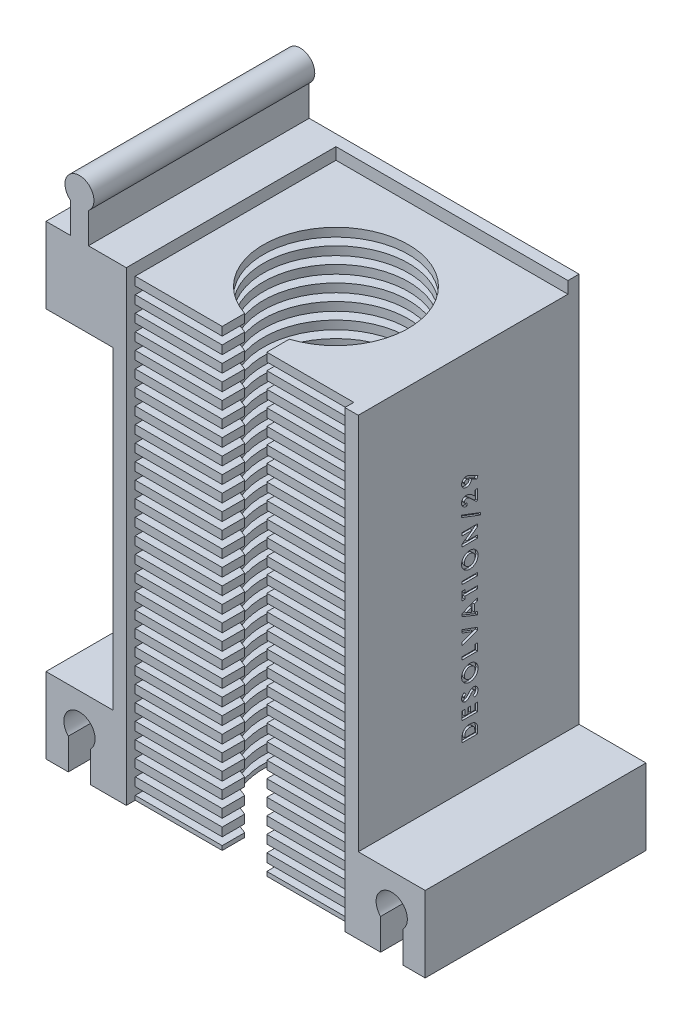
SolidWorks part; units mm, degrees
ref_plane "Plan de face" through (0, 0, 0) normal (0, 0, 1) x (1, 0, 0)
ref_plane "Plan de dessus" through (0, 0, 0) normal (0, 1, 0) x (1, 0, 0)
ref_plane "Plan de droite" through (0, 0, 0) normal (1, 0, 0) x (0, 0, -1)
sketch "Esquisse1" plane through (0, 0, 0) normal (0, 0, 1) x (1, 0, 0)
  line L1 (-20.1477, 24.3067) -> (34.8523, 24.3067)
  line L2 (-20.1477, 24.3067) -> (-20.1477, -82.2433)
  line L3 (-20.1477, -82.2433) -> (34.8523, -82.2433)
  line L4 (34.8523, 24.3067) -> (34.8523, -82.2433)
  dimension "D1" = 55
  dimension "D2" = 106.55
extrude "Boss.-Extru.2" add sketch "Esquisse1" along normal blind 49.5
sketch "Esquisse6" plane through (0, 0, 49.5) normal (0, 0, 1) x (1, 0, 0)
  line L0 (-20.1477, -82.2433) -> (34.8523, -82.2433) construction
  line L1 (-17.1477, 19.5067) -> (31.8523, 19.5067)
  line L2 (-17.1477, 19.5067) -> (-17.1477, -82.2433)
  line L3 (-17.1477, -82.2433) -> (31.8523, -82.2433)
  line L4 (31.8523, 19.5067) -> (31.8523, -82.2433)
  line L5 (-20.1477, 24.3067) -> (-20.1477, -82.2433) construction
  dimension "D1" = 49
  dimension "D2" = 3
  dimension "D3" = 101.75
extrude "Enlèv. mat.-Extru.2" cut sketch "Esquisse6" against normal blind 47
sketch "Esquisse7" plane through (0, 0, 2.5) normal (0, 0, 1) x (1, 0, 0)
  line L0 (31.8523, -82.2433) -> (31.8523, 19.5067) construction
  line L1 (-17.1477, -82.2433) -> (31.8523, -82.2433)
  line L2 (-17.1477, -82.2433) -> (-17.1477, -80.3433)
  line L3 (-17.1477, -80.3433) -> (31.8523, -80.3433)
  line L4 (31.8523, -82.2433) -> (31.8523, -80.3433)
  line L5 (-17.1477, -78.6433) -> (-17.1477, -76.7433)
  line L6 (-17.1477, -78.6433) -> (31.8523, -78.6433)
  line L7 (31.8523, -78.6433) -> (31.8523, -76.7433)
  line L8 (-17.1477, -76.7433) -> (31.8523, -76.7433)
  line L9 (-17.1477, -75.0433) -> (-17.1477, -73.1433)
  line L10 (-17.1477, -75.0433) -> (31.8523, -75.0433)
  line L11 (31.8523, -75.0433) -> (31.8523, -73.1433)
  line L12 (-17.1477, -73.1433) -> (31.8523, -73.1433)
  line L13 (-17.1477, -71.4433) -> (-17.1477, -69.5433)
  line L14 (-17.1477, -71.4433) -> (31.8523, -71.4433)
  line L15 (31.8523, -71.4433) -> (31.8523, -69.5433)
  line L16 (-17.1477, -69.5433) -> (31.8523, -69.5433)
  line L17 (-17.1477, -67.8433) -> (-17.1477, -65.9433)
  line L18 (-17.1477, -67.8433) -> (31.8523, -67.8433)
  line L19 (31.8523, -67.8433) -> (31.8523, -65.9433)
  line L20 (-17.1477, -65.9433) -> (31.8523, -65.9433)
  line L21 (-17.1477, -64.2433) -> (-17.1477, -62.3433)
  line L22 (-17.1477, -64.2433) -> (31.8523, -64.2433)
  line L23 (31.8523, -64.2433) -> (31.8523, -62.3433)
  line L24 (-17.1477, -62.3433) -> (31.8523, -62.3433)
  line L25 (-17.1477, -60.6433) -> (-17.1477, -58.7433)
  line L26 (-17.1477, -60.6433) -> (31.8523, -60.6433)
  line L27 (31.8523, -60.6433) -> (31.8523, -58.7433)
  line L28 (-17.1477, -58.7433) -> (31.8523, -58.7433)
  line L29 (-17.1477, -57.0433) -> (-17.1477, -55.1433)
  line L30 (-17.1477, -57.0433) -> (31.8523, -57.0433)
  line L31 (31.8523, -57.0433) -> (31.8523, -55.1433)
  line L32 (-17.1477, -55.1433) -> (31.8523, -55.1433)
  line L33 (-17.1477, -53.4433) -> (-17.1477, -51.5433)
  line L34 (-17.1477, -53.4433) -> (31.8523, -53.4433)
  line L35 (31.8523, -53.4433) -> (31.8523, -51.5433)
  line L36 (-17.1477, -51.5433) -> (31.8523, -51.5433)
  line L37 (-17.1477, -49.8433) -> (-17.1477, -47.9433)
  line L38 (-17.1477, -49.8433) -> (31.8523, -49.8433)
  line L39 (31.8523, -49.8433) -> (31.8523, -47.9433)
  line L40 (-17.1477, -47.9433) -> (31.8523, -47.9433)
  line L41 (-17.1477, -46.2433) -> (-17.1477, -44.3433)
  line L42 (-17.1477, -46.2433) -> (31.8523, -46.2433)
  line L43 (31.8523, -46.2433) -> (31.8523, -44.3433)
  line L44 (-17.1477, -44.3433) -> (31.8523, -44.3433)
  line L45 (-17.1477, -42.6433) -> (-17.1477, -40.7433)
  line L46 (-17.1477, -42.6433) -> (31.8523, -42.6433)
  line L47 (31.8523, -42.6433) -> (31.8523, -40.7433)
  line L48 (-17.1477, -40.7433) -> (31.8523, -40.7433)
  line L49 (-17.1477, -39.0433) -> (-17.1477, -37.1433)
  line L50 (-17.1477, -39.0433) -> (31.8523, -39.0433)
  line L51 (31.8523, -39.0433) -> (31.8523, -37.1433)
  line L52 (-17.1477, -37.1433) -> (31.8523, -37.1433)
  line L53 (-17.1477, -35.4433) -> (-17.1477, -33.5433)
  line L54 (-17.1477, -35.4433) -> (31.8523, -35.4433)
  line L55 (31.8523, -35.4433) -> (31.8523, -33.5433)
  line L56 (-17.1477, -33.5433) -> (31.8523, -33.5433)
  line L57 (-17.1477, -31.8433) -> (-17.1477, -29.9433)
  line L58 (-17.1477, -31.8433) -> (31.8523, -31.8433)
  line L59 (31.8523, -31.8433) -> (31.8523, -29.9433)
  line L60 (-17.1477, -29.9433) -> (31.8523, -29.9433)
  line L61 (-17.1477, -28.2433) -> (-17.1477, -26.3433)
  line L62 (-17.1477, -28.2433) -> (31.8523, -28.2433)
  line L63 (31.8523, -28.2433) -> (31.8523, -26.3433)
  line L64 (-17.1477, -26.3433) -> (31.8523, -26.3433)
  line L65 (-17.1477, -24.6433) -> (-17.1477, -22.7433)
  line L66 (-17.1477, -24.6433) -> (31.8523, -24.6433)
  line L67 (31.8523, -24.6433) -> (31.8523, -22.7433)
  line L68 (-17.1477, -22.7433) -> (31.8523, -22.7433)
  line L69 (-17.1477, -21.0433) -> (-17.1477, -19.1433)
  line L70 (-17.1477, -21.0433) -> (31.8523, -21.0433)
  line L71 (31.8523, -21.0433) -> (31.8523, -19.1433)
  line L72 (-17.1477, -19.1433) -> (31.8523, -19.1433)
  line L73 (-17.1477, -17.4433) -> (-17.1477, -15.5433)
  line L74 (-17.1477, -17.4433) -> (31.8523, -17.4433)
  line L75 (31.8523, -17.4433) -> (31.8523, -15.5433)
  line L76 (-17.1477, -15.5433) -> (31.8523, -15.5433)
  line L77 (-17.1477, -13.8433) -> (-17.1477, -11.9433)
  line L78 (-17.1477, -13.8433) -> (31.8523, -13.8433)
  line L79 (31.8523, -13.8433) -> (31.8523, -11.9433)
  line L80 (-17.1477, -11.9433) -> (31.8523, -11.9433)
  line L81 (-17.1477, -10.2433) -> (-17.1477, -8.3433)
  line L82 (-17.1477, -10.2433) -> (31.8523, -10.2433)
  line L83 (31.8523, -10.2433) -> (31.8523, -8.3433)
  line L84 (-17.1477, -8.3433) -> (31.8523, -8.3433)
  line L85 (-17.1477, -6.6433) -> (-17.1477, -4.7433)
  line L86 (-17.1477, -6.6433) -> (31.8523, -6.6433)
  line L87 (31.8523, -6.6433) -> (31.8523, -4.7433)
  line L88 (-17.1477, -4.7433) -> (31.8523, -4.7433)
  line L89 (-17.1477, -3.0433) -> (-17.1477, -1.1433)
  line L90 (-17.1477, -3.0433) -> (31.8523, -3.0433)
  line L91 (31.8523, -3.0433) -> (31.8523, -1.1433)
  line L92 (-17.1477, -1.1433) -> (31.8523, -1.1433)
  line L93 (-17.1477, 0.5567) -> (-17.1477, 2.4567)
  line L94 (-17.1477, 0.5567) -> (31.8523, 0.5567)
  line L95 (31.8523, 0.5567) -> (31.8523, 2.4567)
  line L96 (-17.1477, 2.4567) -> (31.8523, 2.4567)
  line L97 (-17.1477, 4.1567) -> (-17.1477, 6.0567)
  line L98 (-17.1477, 4.1567) -> (31.8523, 4.1567)
  line L99 (31.8523, 4.1567) -> (31.8523, 6.0567)
  line L100 (-17.1477, 6.0567) -> (31.8523, 6.0567)
  line L101 (-17.1477, 7.7567) -> (-17.1477, 9.6567)
  line L102 (-17.1477, 7.7567) -> (31.8523, 7.7567)
  line L103 (31.8523, 7.7567) -> (31.8523, 9.6567)
  line L104 (-17.1477, 9.6567) -> (31.8523, 9.6567)
  line L105 (-17.1477, 11.3567) -> (-17.1477, 13.2567)
  line L106 (-17.1477, 11.3567) -> (31.8523, 11.3567)
  line L107 (31.8523, 11.3567) -> (31.8523, 13.2567)
  line L108 (-17.1477, 13.2567) -> (31.8523, 13.2567)
  line L109 (-17.1477, 14.9567) -> (-17.1477, 16.8567)
  line L110 (-17.1477, 14.9567) -> (31.8523, 14.9567)
  line L111 (31.8523, 14.9567) -> (31.8523, 16.8567)
  line L112 (-17.1477, 16.8567) -> (31.8523, 16.8567)
  line L113 (-17.1477, 18.5567) -> (-17.1477, 20.4567)
  line L114 (-17.1477, 18.5567) -> (31.8523, 18.5567)
  line L115 (31.8523, 18.5567) -> (31.8523, 20.4567)
  line L116 (-17.1477, 20.4567) -> (31.8523, 20.4567)
  dimension "D1" = 1.9
  dimension "D2" = 29
extrude "Boss.-Extru.3" add sketch "Esquisse7" along normal blind 45
sketch "Esquisse8" plane through (0, -82.2433, 0) normal (0, -1, 0) x (1, 0, 0)
  line L0 (-17.1477, 47.5) -> (-17.1477, 49.5) construction
  line L1 (-20.1477, 49.5) -> (-20.1477, 0) construction
  circle A0 centre (7.3523, 27) radius 16.25
  point P4 (-17.1477, 48.5)
  dimension "D1" = 32.5
  dimension "D2" = 21.5
  dimension "D3" = 27.5
extrude "Enlèv. mat.-Extru.4" cut sketch "Esquisse8" against normal through all
sketch "Esquisse9" plane through (0, -82.2433, 0) normal (0, -1, 0) x (1, 0, 0)
  line L0 (2.3523, 47.5) -> (2.3523, 42.4616)
  line L1 (-17.1477, 47.5) -> (31.8523, 47.5) construction
  line L2 (12.3523, 47.5) -> (12.3523, 42.4616)
  line L3 (2.3523, 47.5) -> (12.3523, 47.5)
  line L4 (-20.1477, 49.5) -> (-20.1477, 0) construction
  line L5 (2.3523, 42.4616) -> (12.3523, 42.4616)
  circle A0 centre (7.3523, 27) radius 16.25 construction
  dimension "D1" = 10
  dimension "D2" = 22.5
extrude "Enlèv. mat.-Extru.5" cut sketch "Esquisse9" against normal through all
sketch "Esquisse10" plane through (0, -82.2433, 0) normal (0, -1, 0) x (1, 0, 0)
  line L11 (31.8523, 47.5) -> (12.3523, 47.5)
  line L12 (12.3523, 47.5) -> (12.3523, 42.4616)
  line L13 (2.3523, 42.4616) -> (2.3523, 47.5)
  line L14 (2.3523, 47.5) -> (-17.1477, 47.5)
  line L15 (-17.1477, 47.5) -> (-17.1477, 49.5)
  line L16 (-17.1477, 49.5) -> (-20.1477, 49.5)
  line L17 (-20.1477, 49.5) -> (-20.1477, 0)
  line L18 (-20.1477, 0) -> (34.8523, 0)
  line L19 (34.8523, 0) -> (34.8523, 49.5)
  line L20 (34.8523, 49.5) -> (31.8523, 49.5)
  line L21 (31.8523, 49.5) -> (31.8523, 47.5)
  line L22 (31.8523, 47.5) -> (12.3523, 47.5)
  line L23 (12.3523, 47.5) -> (12.3523, 42.4616)
  line L24 (2.3523, 42.4616) -> (2.3523, 47.5)
  line L25 (2.3523, 47.5) -> (-17.1477, 47.5)
  line L26 (-17.1477, 47.5) -> (-17.1477, 49.5)
  line L27 (-17.1477, 49.5) -> (-20.1477, 49.5)
  line L28 (-20.1477, 49.5) -> (-20.1477, 0)
  line L29 (-20.1477, 0) -> (34.8523, 0)
  line L30 (34.8523, 0) -> (34.8523, 49.5)
  line L31 (34.8523, 49.5) -> (31.8523, 49.5)
  line L32 (31.8523, 49.5) -> (31.8523, 47.5)
  arc A1 (2.3523, 42.4616) -> (12.3523, 42.4616) centre (7.3523, 27) ccw
  arc A2 (2.3523, 42.4616) -> (12.3523, 42.4616) centre (7.3523, 27) ccw
  dimension "D1" = 0
sketch "Esquisse11" plane through (0, 24.3067, 0) normal (0, 1, 0) x (1, 0, 0)
  line L4 (34.8523, 0) -> (-20.1477, 0)
  line L5 (-20.1477, 0) -> (-20.1477, -49.5)
  line L6 (-20.1477, -49.5) -> (34.8523, -49.5)
  line L7 (34.8523, -49.5) -> (34.8523, 0)
  line L8 (34.8523, 0) -> (-20.1477, 0)
  line L9 (-20.1477, 0) -> (-20.1477, -49.5)
  line L10 (-20.1477, -49.5) -> (34.8523, -49.5)
  line L11 (34.8523, -49.5) -> (34.8523, 0)
  dimension "D1" = 0
extrude "Enlèv. mat.-Extru.6" cut sketch "Esquisse11" against normal blind 4.8
sketch "Esquisse14" plane through (0, 0, 49.5) normal (0, 0, 1) x (1, 0, 0)
  line L1 (34.8523, -82.2433) -> (49.8523, -82.2433)
  line L2 (34.8523, -82.2433) -> (34.8523, -64.2933)
  line L3 (34.8523, -64.2933) -> (49.8523, -64.2933)
  line L4 (49.8523, -82.2433) -> (49.8523, -64.2933)
  dimension "D1" = 15
  dimension "D2" = 17.95
extrude "Boss.-Extru.5" add sketch "Esquisse14" against normal up to surface (49.5 mm away) up to face at (7.3523, -31.3683, 0)
sketch "Esquisse15" plane through (0, 0, 49.5) normal (0, 0, 1) x (1, 0, 0)
  line L1 (-20.1477, -82.2433) -> (-35.1477, -82.2433)
  line L2 (-20.1477, -82.2433) -> (-20.1477, -64.2933)
  line L3 (-20.1477, -64.2933) -> (-35.1477, -64.2933)
  line L4 (-35.1477, -82.2433) -> (-35.1477, -64.2933)
  dimension "D1" = 17.95
  dimension "D2" = 15
extrude "Boss.-Extru.6" add sketch "Esquisse15" against normal up to surface (49.5 mm away) up to face at (21.5189, -42.3433, 0)
sketch "Esquisse16" plane through (0, 0, 49.5) normal (0, 0, 1) x (1, 0, 0)
  line L1 (34.8523, 19.5067) -> (49.8523, 19.5067)
  line L2 (34.8523, 19.5067) -> (34.8523, 2.5067)
  line L3 (34.8523, 2.5067) -> (49.8523, 2.5067)
  line L4 (49.8523, 19.5067) -> (49.8523, 2.5067)
  dimension "D1" = 17
  dimension "D2" = 15
extrude "Boss.-Extru.7" add sketch "Esquisse16" against normal up to surface (49.5 mm away) up to face at (7.3523, -47.8308, 0)
sketch "Esquisse17" plane through (0, 0, 49.5) normal (0, 0, 1) x (1, 0, 0)
  line L1 (-20.1477, 19.5067) -> (-35.1477, 19.5067)
  line L2 (-20.1477, 19.5067) -> (-20.1477, 2.5067)
  line L3 (-20.1477, 2.5067) -> (-35.1477, 2.5067)
  line L4 (-35.1477, 19.5067) -> (-35.1477, 2.5067)
  dimension "D1" = 15
  dimension "D2" = 17
extrude "Boss.-Extru.8" add sketch "Esquisse17" against normal up to surface (49.5 mm away) up to face at (15.8523, -37.7633, 0)
sketch "Esquisse18" plane through (0, 0, 49.5) normal (0, 0, 1) x (1, 0, 0)
  line L0 (44.8523, -74.3433) -> (44.8523, -82.2433)
  line L2 (44.8523, -82.2433) -> (39.8523, -82.2433)
  line L3 (39.8523, -82.2433) -> (39.8523, -74.3433)
  line L4 (7.3523, -82.2443) -> (7.3523, -64.1566) construction
  line L5 (49.8523, -82.2433) -> (49.8523, -64.2933) construction
  line L7 (-30.1477, -82.2433) -> (-25.1477, -82.2433)
  line L8 (-30.1477, -74.3433) -> (-30.1477, -82.2433)
  line L9 (-25.1477, -82.2433) -> (-25.1477, -74.3433)
  line L15 (31.8523, -82.2433) -> (49.8523, -82.2433) construction
  arc A0 (44.8523, -74.3433) -> (39.8523, -74.3433) centre (42.3523, -71.8938) ccw
  arc A1 (-30.1477, -74.3433) -> (-25.1477, -74.3433) centre (-27.6477, -71.8938) cw
  dimension "D5" = 3.5
  dimension "D1" = 5
  dimension "D2" = 5
  dimension "D3" = 7.9
  dimension "D4" = 7.9
extrude "Enlèv. mat.-Extru.8" cut sketch "Esquisse18" against normal through all
sketch "Esquisse20" plane through (0, 0, 49.5) normal (0, 0, 1) x (1, 0, 0)
  line L0 (-29.6477, 29.9467) -> (-29.6477, 19.5067)
  line L1 (-35.1477, 19.5067) -> (-17.1477, 19.5067) construction
  line L2 (-29.6477, 19.5067) -> (-25.6477, 19.5067)
  line L3 (-25.6477, 19.5067) -> (-25.6477, 29.9467)
  line L4 (-35.1477, 19.5067) -> (-35.1477, 2.5067) construction
  line L5 (7.3523, 19.5067) -> (7.3523, 35.4205) construction
  line L6 (23.6023, 19.5067) -> (-8.8977, 19.5067) construction
  line L7 (40.3523, 19.5067) -> (40.3523, 29.9467)
  line L8 (44.3523, 19.5067) -> (40.3523, 19.5067)
  line L9 (44.3523, 29.9467) -> (44.3523, 19.5067)
  arc A0 (-25.6477, 29.9467) -> (-29.6477, 29.9467) centre (-27.6477, 32.5084) ccw
  arc A1 (40.3523, 29.9467) -> (44.3523, 29.9467) centre (42.3523, 32.5084) cw
  dimension "D3" = 3.25
  dimension "D1" = 5.5
  dimension "D2" = 4
  dimension "D4" = 10.44
  dimension "D5" = 10.44
extrude "Boss.-Extru.9" add sketch "Esquisse20" against normal up to surface (49.5 mm away) up to face at (7.3523, -49.3534, 0)
extrude "Enlèv. mat.-Extru.10" cut sketch "Esquisse10" against normal blind 0.95
sketch "Esquisse22" plane through (0, -82.2433, 0) normal (0, -1, 0) x (1, 0, 0)
  line L0 (49.8523, 49.5) -> (44.8523, 49.5) construction
  line L1 (44.8523, 49.5) -> (44.8523, 0) construction
  line L2 (44.8523, 0) -> (49.8523, 0) construction
  line L3 (49.8523, 0) -> (49.8523, 49.5) construction
  line L4 (39.8523, 49.5) -> (34.8523, 49.5) construction
  line L5 (34.8523, 49.5) -> (34.8523, 0) construction
  line L6 (34.8523, 0) -> (39.8523, 0) construction
  line L7 (39.8523, 0) -> (39.8523, 49.5) construction
  line L8 (-35.1477, 0) -> (-30.1477, 0) construction
  line L9 (-30.1477, 0) -> (-30.1477, 49.5) construction
  line L10 (-30.1477, 49.5) -> (-35.1477, 49.5) construction
  line L11 (-35.1477, 49.5) -> (-35.1477, 0) construction
  line L12 (-25.1477, 0) -> (-20.1477, 0) construction
  line L13 (-20.1477, 0) -> (-20.1477, 49.5) construction
  line L14 (-20.1477, 49.5) -> (-25.1477, 49.5) construction
  line L15 (-25.1477, 49.5) -> (-25.1477, 0) construction
  line L16 (49.8523, 49.5) -> (44.8523, 49.5)
  line L17 (44.8523, 49.5) -> (44.8523, 0)
  line L18 (44.8523, 0) -> (49.8523, 0)
  line L19 (49.8523, 0) -> (49.8523, 49.5)
  line L20 (39.8523, 49.5) -> (34.8523, 49.5)
  line L21 (34.8523, 49.5) -> (34.8523, 0)
  line L22 (34.8523, 0) -> (39.8523, 0)
  line L23 (39.8523, 0) -> (39.8523, 49.5)
  line L24 (-35.1477, 0) -> (-30.1477, 0)
  line L25 (-30.1477, 0) -> (-30.1477, 49.5)
  line L26 (-30.1477, 49.5) -> (-35.1477, 49.5)
  line L27 (-35.1477, 49.5) -> (-35.1477, 0)
  line L28 (-25.1477, 0) -> (-20.1477, 0)
  line L29 (-20.1477, 0) -> (-20.1477, 49.5)
  line L30 (-20.1477, 49.5) -> (-25.1477, 49.5)
  line L31 (-25.1477, 49.5) -> (-25.1477, 0)
extrude "Enlèv. mat.-Extru.11" cut sketch "Esquisse22" against normal up to surface (0.95 mm away) up to face at (7.3523, -81.2933, 36.7676)
sketch "Esquisse23" plane through (0, 19.5067, 0) normal (0, 1, 0) x (1, 0, 0)
  line L11 (40.3523, -49.5) -> (40.3523, 0)
  line L12 (40.3523, 0) -> (-25.6477, 0)
  line L13 (-25.6477, 0) -> (-25.6477, -49.5)
  line L14 (-25.6477, -49.5) -> (-17.1477, -49.5)
  line L15 (-17.1477, -49.5) -> (-17.1477, -47.5)
  line L16 (-17.1477, -47.5) -> (2.3523, -47.5)
  line L17 (2.3523, -47.5) -> (2.3523, -42.4616)
  line L18 (12.3523, -42.4616) -> (12.3523, -47.5)
  line L19 (12.3523, -47.5) -> (31.8523, -47.5)
  line L20 (31.8523, -47.5) -> (31.8523, -49.5)
  line L21 (31.8523, -49.5) -> (40.3523, -49.5)
  line L22 (40.3523, -49.5) -> (40.3523, 0)
  line L23 (40.3523, 0) -> (-25.6477, 0)
  line L24 (-25.6477, 0) -> (-25.6477, -49.5)
  line L25 (-25.6477, -49.5) -> (-17.1477, -49.5)
  line L26 (-17.1477, -49.5) -> (-17.1477, -47.5)
  line L27 (-17.1477, -47.5) -> (2.3523, -47.5)
  line L28 (2.3523, -47.5) -> (2.3523, -42.4616)
  line L29 (12.3523, -42.4616) -> (12.3523, -47.5)
  line L30 (12.3523, -47.5) -> (31.8523, -47.5)
  line L31 (31.8523, -47.5) -> (31.8523, -49.5)
  line L32 (31.8523, -49.5) -> (40.3523, -49.5)
  arc A1 (12.3523, -42.4616) -> (2.3523, -42.4616) centre (7.3523, -27) ccw
  arc A2 (12.3523, -42.4616) -> (2.3523, -42.4616) centre (7.3523, -27) ccw
  dimension "D1" = 0
extrude "Boss.-Extru.10" add sketch "Esquisse23" along normal blind 3.6
sketch "Esquisse24" plane through (0, 0, 47.5) normal (0, 0, 1) x (1, 0, 0)
  line L0 (-17.1477, 23.1067) -> (-17.1477, 18.5567) construction
  line L1 (31.8523, 20.4567) -> (-17.1477, 20.4567)
  line L2 (31.8523, 20.4567) -> (31.8523, 22.1567)
  line L3 (31.8523, 22.1567) -> (-17.1477, 22.1567)
  line L4 (-17.1477, 20.4567) -> (-17.1477, 22.1567)
  line L5 (31.8523, 20.4567) -> (-17.1477, 22.1567) construction
  line L6 (31.8523, 22.1567) -> (-17.1477, 20.4567) construction
  line L7 (31.8523, 18.5567) -> (31.8523, 23.1067) construction
  line L8 (-17.1477, 23.1067) -> (2.3523, 23.1067) construction
  point P0 (7.3523, 21.3067)
  dimension "D1" = 1.7
  dimension "D2" = 0.95
extrude "Enlèv. mat.-Extru.12" cut sketch "Esquisse24" against normal up to surface (45 mm away) up to face at (7.3523, 17.7067, 2.5)
sketch "Esquisse25" plane through (0, 2.5067, 0) normal (0, -1, 0) x (1, 0, 0)
  line L4 (-35.1477, 0) -> (-20.1477, 0)
  line L5 (-20.1477, 0) -> (-20.1477, 49.5)
  line L6 (-20.1477, 49.5) -> (-35.1477, 49.5)
  line L7 (-35.1477, 49.5) -> (-35.1477, 0)
  line L8 (-35.1477, 0) -> (-20.1477, 0)
  line L9 (-20.1477, 0) -> (-20.1477, 49.5)
  line L10 (-20.1477, 49.5) -> (-35.1477, 49.5)
  line L11 (-35.1477, 49.5) -> (-35.1477, 0)
  line L12 (34.8523, 0) -> (49.8523, 0)
  line L13 (49.8523, 0) -> (49.8523, 49.5)
  line L14 (49.8523, 49.5) -> (34.8523, 49.5)
  line L15 (34.8523, 49.5) -> (34.8523, 0)
  line L16 (34.8523, 0) -> (49.8523, 0)
  line L17 (49.8523, 0) -> (49.8523, 49.5)
  line L18 (49.8523, 49.5) -> (34.8523, 49.5)
  line L19 (34.8523, 49.5) -> (34.8523, 0)
  dimension "D1" = 0
  dimension "D2" = 0
extrude "Enlèv. mat.-Extru.13" cut sketch "Esquisse25" against normal blind 3.6
sketch "Esquisse26" plane through (0, 19.5067, 0) normal (0, 1, 0) x (1, 0, 0)
  line L4 (-29.6477, -49.5) -> (-29.6477, 0)
  line L5 (-29.6477, 0) -> (-35.1477, 0)
  line L6 (-35.1477, 0) -> (-35.1477, -49.5)
  line L7 (-35.1477, -49.5) -> (-29.6477, -49.5)
  line L8 (-29.6477, -49.5) -> (-29.6477, 0)
  line L9 (-29.6477, 0) -> (-35.1477, 0)
  line L10 (-35.1477, 0) -> (-35.1477, -49.5)
  line L11 (-35.1477, -49.5) -> (-29.6477, -49.5)
  line L12 (44.3523, 0) -> (44.3523, -49.5)
  line L13 (44.3523, -49.5) -> (49.8523, -49.5)
  line L14 (49.8523, -49.5) -> (49.8523, 0)
  line L15 (49.8523, 0) -> (44.3523, 0)
  line L16 (44.3523, 0) -> (44.3523, -49.5)
  line L17 (44.3523, -49.5) -> (49.8523, -49.5)
  line L18 (49.8523, -49.5) -> (49.8523, 0)
  line L19 (49.8523, 0) -> (44.3523, 0)
  dimension "D1" = 0
  dimension "D2" = 0
extrude "Boss.-Extru.11" add sketch "Esquisse26" along normal blind 3.6
sketch "Esquisse27" plane through (34.8523, 0, 0) normal (1, 0, 0) x (0, 0, -1)
  line L0 (-22.75, -64.2933) -> (-22.75, 6.1067) construction
  line L4 (-49.5, -64.2933) -> (-49.5, 6.1067) construction
  text T0 "<b>DESOLVATION/29</b>" font "Century Gothic" height 3.5
  dimension "D1" = 26.75
extrude "Enlèv. mat.-Extru.14" cut sketch "Esquisse27" against normal blind 0.5
sketch "Esquisse28" plane through (0, 6.1067, 0) normal (0, -1, 0) x (1, 0, 0)
  line L4 (34.8523, 49.5) -> (34.8523, 0)
  line L5 (34.8523, 0) -> (49.8523, 0)
  line L6 (49.8523, 0) -> (49.8523, 49.5)
  line L7 (49.8523, 49.5) -> (34.8523, 49.5)
  line L8 (34.8523, 49.5) -> (34.8523, 0)
  line L9 (34.8523, 0) -> (49.8523, 0)
  line L10 (49.8523, 0) -> (49.8523, 49.5)
  line L11 (49.8523, 49.5) -> (34.8523, 49.5)
  dimension "D1" = 0
extrude "Enlèv. mat.-Extru.15" cut sketch "Esquisse28" against normal through all
sketch "Esquisse29" plane through (-17.1477, 0, 0) normal (1, 0, 0) x (0, 0, -1)
  line L1 (-2.5, 20.4567) -> (-49.5, 20.4567)
  line L2 (-2.5, 20.4567) -> (-2.5, 23.1067)
  line L3 (-2.5, 23.1067) -> (-49.5, 23.1067)
  line L4 (-49.5, 20.4567) -> (-49.5, 23.1067)
  point P6 (0, 0)
  point P7 (0, 0)
extrude "Enlèv. mat.-Extru.16" cut sketch "Esquisse29" along normal through all
